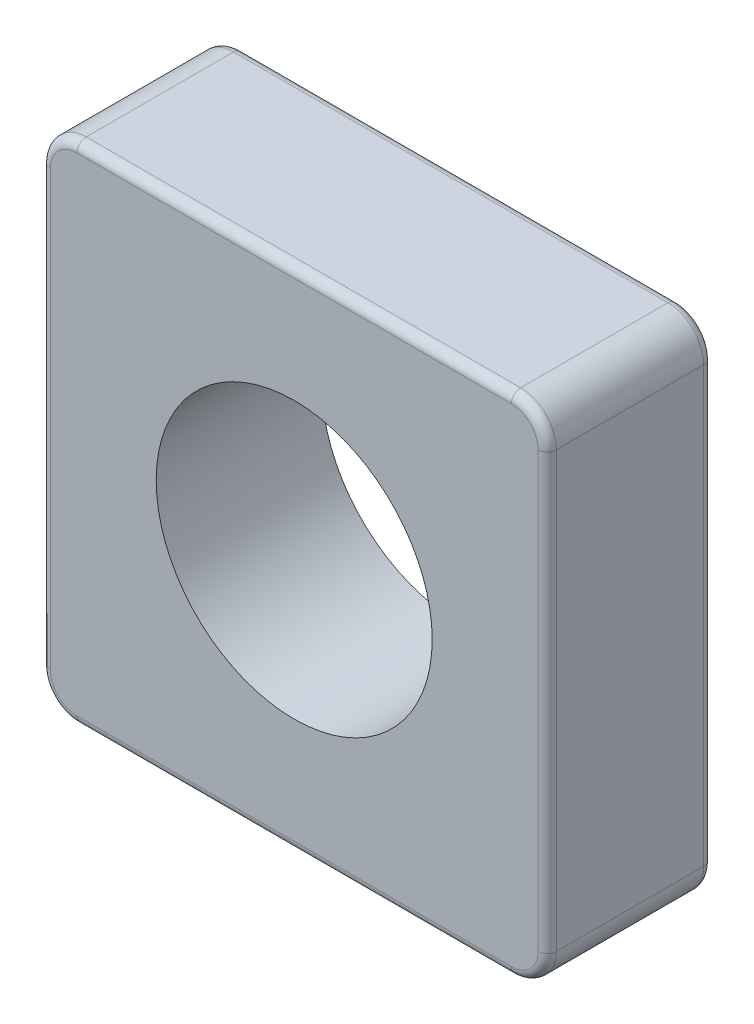
SolidWorks part; units mm, degrees
ref_plane "Front Plane" through (0, 0, 0) normal (1, 0, 0) x (0, 1, 0)
ref_plane "Top Plane" through (0, 0, 0) normal (0, 0, 1) x (0, 1, 0)
ref_plane "Right Plane" through (0, 0, 0) normal (0, 1, 0) x (-1, 0, 0)
sketch "Sketch1" plane through (0, 0, 0) normal (0, 0, 1) x (0, 1, 0)
  line L1 (-2.75, -2.75) -> (2.75, -2.75)
  line L2 (-2.75, -2.75) -> (-2.75, 2.75)
  line L3 (-2.75, 2.75) -> (2.75, 2.75)
  line L4 (2.75, -2.75) -> (2.75, 2.75)
  line L5 (-2.75, -2.75) -> (2.75, 2.75) construction
  line L6 (-2.75, 2.75) -> (2.75, -2.75) construction
  circle A0 centre (0, 0) radius 1.5
  dimension "D1" = 3
  dimension "D2" = 5.5
  dimension "D3" = 5.5
extrude "Boss-Extrude1" add sketch "Sketch1" along normal blind 1.8
fillet "Fillet1" radius 0.3891 4 edges at (-2.75, -2.75, 0.9) (-2.75, 2.75, 0.9) (2.75, 2.75, 0.9) (2.75, -2.75, 0.9)
thread "Thread1" pitch 0.5 start angle 0, offset 1, length 0, pitch 0.5, diameter 3
ref_plane "Plane1" through (-1.5, 0, 2.8) normal (0, -1, 0) x (-1, 0, 0)
sketch "Thread Profile1" plane through (-1.5, 0, 2.8) normal (0, -1, 0) x (-1, 0, 0)
  line L0 (0, 0) -> (0, 0.5) construction
  line L11 (0, 0) -> (0, 0.4375)
  line L12 (0, 0.4375) -> (-0.2706, 0.2812)
  line L13 (-0.2706, 0.2812) -> (-0.2706, 0.1562)
  line L15 (-0.2706, 0.1562) -> (0, 0)
  line L17 (-0.2706, 0.2187) -> (0, 0.2187) construction
  point P2 (0, 0)
  dimension "Pitch" = 0.5
  dimension "Profile_Angle" = 60
  dimension "Profile_Land" = 0.125
  dimension "Profile_Height" = 0.2706
fillet "Fillet2" radius 0.1 16 edges at (-2.636, -2.636, 0) (-2.75, 0, 0) (-2.636, 2.636, 0) (0, 2.75, 0) (2.636, 2.636, 0) (2.75, 0, 0) (2.636, -2.636, 0) (-2.636, -2.636, 1.8) (-2.75, 0, 1.8) (-2.636, 2.636, 1.8) (0, 2.75, 1.8) (2.636, 2.636, 1.8) (2.75, 0, 1.8) (2.636, -2.636, 1.8) (0, -2.75, 0) (0, -2.75, 1.8)
equation "\"D1@Fillet1\"=(5.5 * 2^0.5 - 7)/2"
